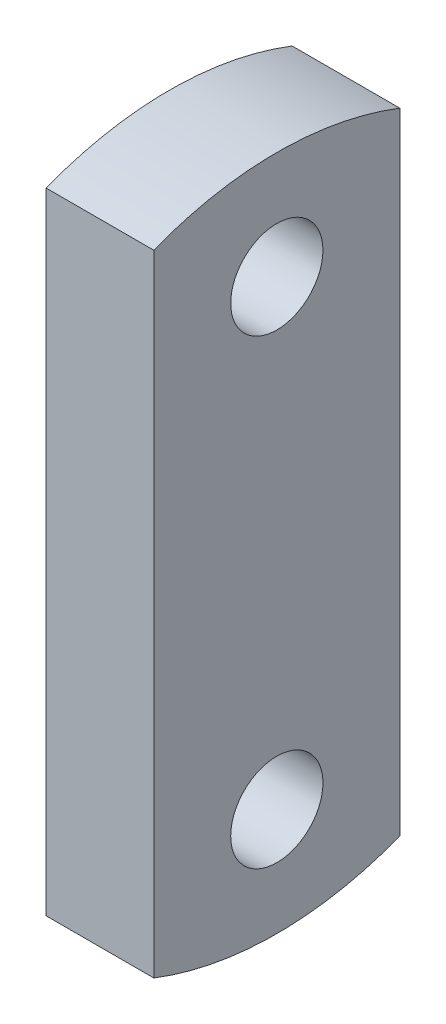
SolidWorks part; units mm, degrees
ref_plane "Front Plane" through (0, 0, 0) normal (0, 0, 1) x (1, 0, 0)
ref_plane "Top Plane" through (0, 0, 0) normal (0, 1, 0) x (1, 0, 0)
ref_plane "Right Plane" through (0, 0, 0) normal (1, 0, 0) x (0, 0, -1)
sketch "Sketch1" plane through (0, 0, 0) normal (1, 0, 0) x (0, 0, -1)
  line L4 (0, 143.1021) -> (0, -165.6589) construction
  line L10 (40, -102.4695) -> (40, 102.4695)
  line L12 (-40, -102.4695) -> (-40, 102.4695)
  line L13 (40, -102.4695) -> (-40, 102.4695) construction
  line L14 (40, 102.4695) -> (-40, -102.4695) construction
  line L15 (-135.8522, 75) -> (113.4926, 75) construction
  line L16 (-135.8522, -75) -> (118.5709, -75) construction
  line L17 (-104.5528, 0) -> (105.7038, 0) construction
  arc A4 (-40, -102.4695) -> (40, -102.4695) centre (0, 0) ccw
  arc A5 (40, 102.4695) -> (-40, 102.4695) centre (0, 0) ccw
  circle A6 centre (0, 75) radius 15
  circle A7 centre (0, -75) radius 15
  dimension "D2" = 80
  dimension "D1" = 220
  dimension "D5" = 30
  dimension "D3" = 150
  dimension "D4" = 75
extrude "Boss-Extrude1" add sketch "Sketch1" along normal blind 35
